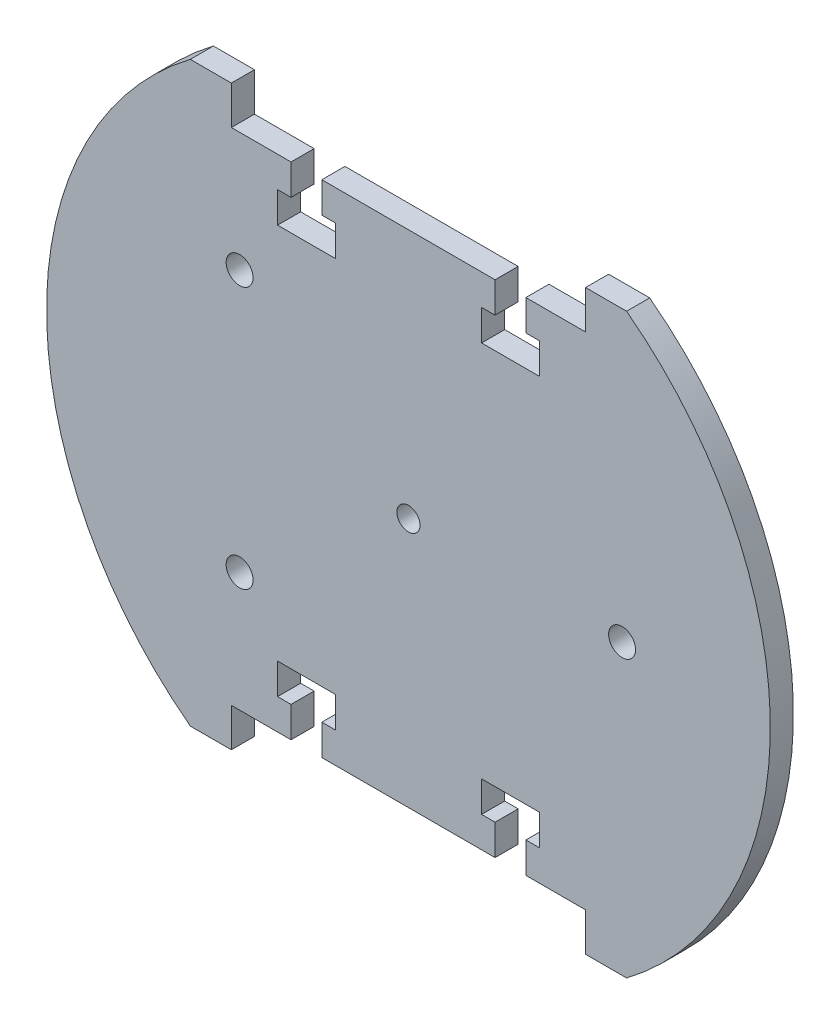
SolidWorks part; units mm, degrees
ref_plane "Front Plane" through (0, 0, 0) normal (0, 0, 1) x (1, 0, 0)
ref_plane "Top Plane" through (0, 0, 0) normal (0, 1, 0) x (1, 0, 0)
ref_plane "Right Plane" through (0, 0, 0) normal (1, 0, 0) x (0, 0, -1)
sketch "Sketch8" plane through (0, 0, 0) normal (0, 0, 1) x (1, 0, 0)
  line L46 (-56.6657, -75) -> (-46, -75)
  line L47 (-30.5, -65) -> (-30.5, -57.0293)
  line L48 (30.5, -57.0293) -> (30.5, -65)
  line L49 (-46, -65) -> (-30.5, -65)
  line L50 (46, -65) -> (46, -75)
  line L52 (-34, 49.0293) -> (-34, 57.0293)
  line L53 (19, -57.0293) -> (19, -49.0293)
  line L54 (-22.5, 65) -> (-22.5, 57.0293)
  line L55 (-30.5, 57.0293) -> (-30.5, 65)
  line L56 (-30.5, 65) -> (-46, 65)
  line L57 (56.6657, 75) -> (46, 75)
  line L58 (-22.5, -57.0293) -> (-22.5, -65)
  line L59 (-46, 65) -> (-46, 75)
  line L60 (30.5, -65) -> (46, -65)
  line L61 (19, 57.0293) -> (22.5, 57.0293)
  line L62 (-34, -57.0293) -> (-34, -49.0293)
  line L63 (34, 49.0293) -> (19, 49.0293)
  line L64 (-19, 49.0293) -> (-34, 49.0293)
  line L65 (34, -49.0293) -> (34, -57.0293)
  line L66 (46, 75) -> (46, 65)
  line L67 (34, 57.0293) -> (34, 49.0293)
  line L68 (-22.5, -65) -> (22.5, -65)
  line L70 (-46, -75) -> (-46, -65)
  line L71 (22.5, -65) -> (22.5, -57.0293)
  line L72 (19, -49.0293) -> (34, -49.0293)
  line L73 (-34, -49.0293) -> (-19, -49.0293)
  line L74 (-46, 75) -> (-56.6657, 75)
  line L75 (-19, -49.0293) -> (-19, -57.0293)
  line L76 (34, -57.0293) -> (30.5, -57.0293)
  line L77 (22.5, 57.0293) -> (22.5, 65)
  line L78 (46, 65) -> (30.5, 65)
  line L80 (22.5, 65) -> (-22.5, 65)
  line L81 (-22.5, 57.0293) -> (-19, 57.0293)
  line L82 (22.5, -57.0293) -> (19, -57.0293)
  line L83 (30.5, 65) -> (30.5, 57.0293)
  line L84 (30.5, 57.0293) -> (34, 57.0293)
  line L85 (-19, 57.0293) -> (-19, 49.0293)
  line L86 (-30.5, -57.0293) -> (-34, -57.0293)
  line L87 (46, -75) -> (56.6657, -75)
  line L88 (19, 49.0293) -> (19, 57.0293)
  line L90 (-34, 57.0293) -> (-30.5, 57.0293)
  line L91 (-19, -57.0293) -> (-22.5, -57.0293)
  line L92 (-125.2624, 0) -> (139.2989, 0) construction
  line L93 (0, 88.7884) -> (0, -98.0596) construction
  line L94 (124.3842, 0) -> (260.3146, 0) construction
  line L95 (0, 88.5153) -> (0, -14.7198) construction
  circle A8 centre (-43.86, 34) radius 3.5
  circle A9 centre (55.5, 0) radius 3.5
  arc A10 (-56.6657, 75) -> (-56.6657, -75) centre (0, 0) ccw
  circle A11 centre (-43.86, -34) radius 3.5
  arc A12 (56.6657, -75) -> (56.6657, 75) centre (0, 0) ccw
  circle A18 centre (0, 0) radius 3
  dimension "D1" = 94
  dimension "D7" = 7
  dimension "D8" = 7
  dimension "D9" = 7
  dimension "D2" = 150
  dimension "D3" = 10
  dimension "D4" = 7.9707
  dimension "D5" = 8
  dimension "D6" = 15
  dimension "D11" = 46
  dimension "D12" = 34
  dimension "D13" = 49.0293
  dimension "D14" = 34
  dimension "D15" = 34
  dimension "D16" = 55.5
extrude "Boss-Extrude3" add sketch "Sketch8" along normal blind 6
